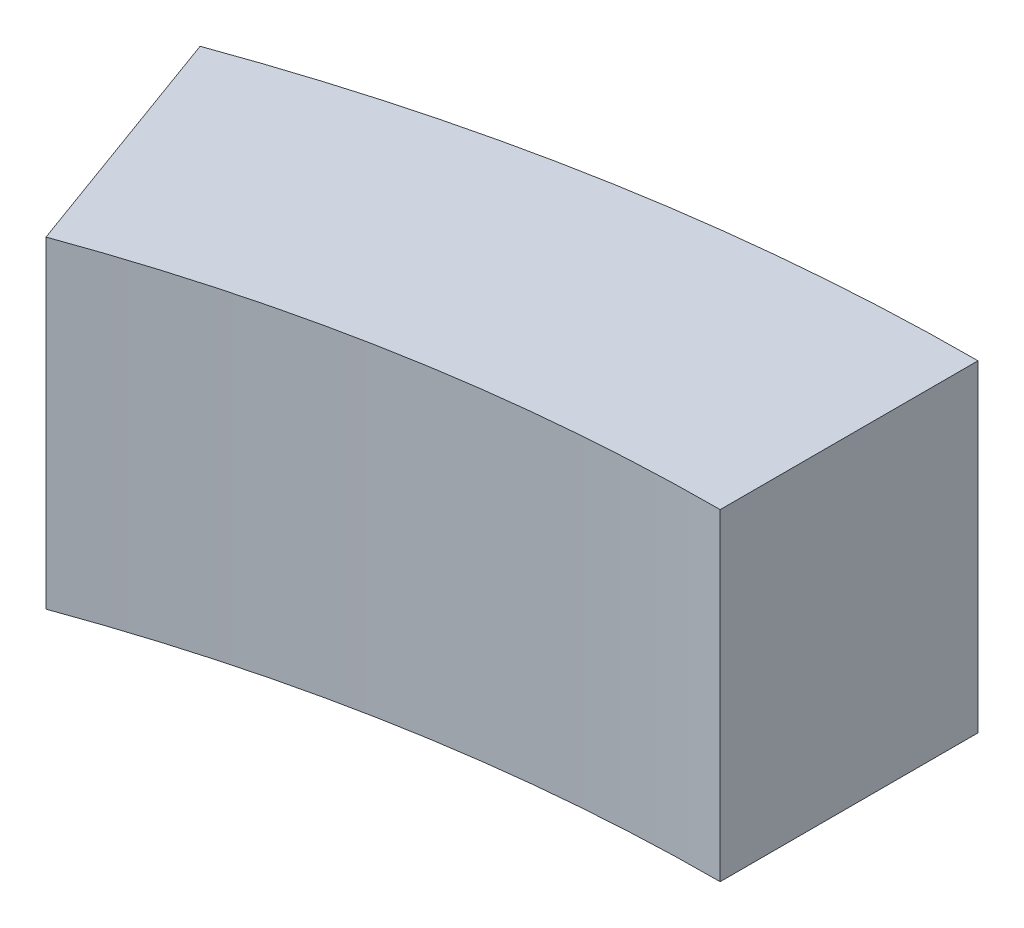
SolidWorks part; units mm, degrees
ref_plane "Ebene vorne" through (0, 0, 0) normal (0, 0, 1) x (1, 0, 0)
ref_plane "Ebene oben" through (0, 0, 0) normal (0, 1, 0) x (1, 0, 0)
ref_plane "Ebene rechts" through (0, 0, 0) normal (1, 0, 0) x (0, 0, -1)
sketch "Skizze1" plane through (0, 0, 0) normal (0, 1, 0) x (1, 0, 0)
  line L0 (-20.5212, 56.3816) -> (-17.785, 48.864)
  line L1 (0, 52) -> (0, 60)
  arc A0 (-20.5212, 56.3816) -> (0, 60) centre (0, 0) cw
  arc A1 (-17.785, 48.864) -> (0, 52) centre (0, 0) cw
  dimension "D1" = 60
  dimension "D3" = 52
  dimension "D2" = 20
extrude "Aufsatz-Linear austragen1" add sketch "Skizze1" along normal blind 10
